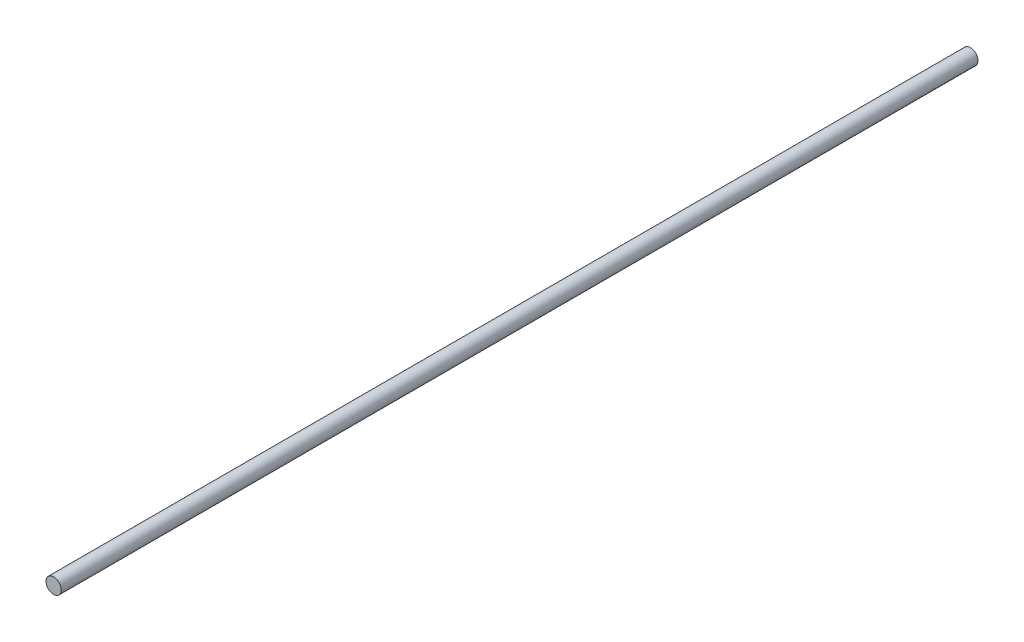
SolidWorks part; units mm, degrees
ref_plane "Plan de face" through (0, 0, 0) normal (0, 0, 1) x (1, 0, 0)
ref_plane "Plan de dessus" through (0, 0, 0) normal (0, 1, 0) x (1, 0, 0)
ref_plane "Plan de droite" through (0, 0, 0) normal (1, 0, 0) x (0, 0, -1)
sketch "Esquisse1" plane through (0, 0, 0) normal (0, 0, 1) x (1, 0, 0)
  circle A0 centre (0, 0) radius 4
  dimension "D1" = 8
extrude "Boss.-Extru.1" add sketch "Esquisse1" along normal blind 480
